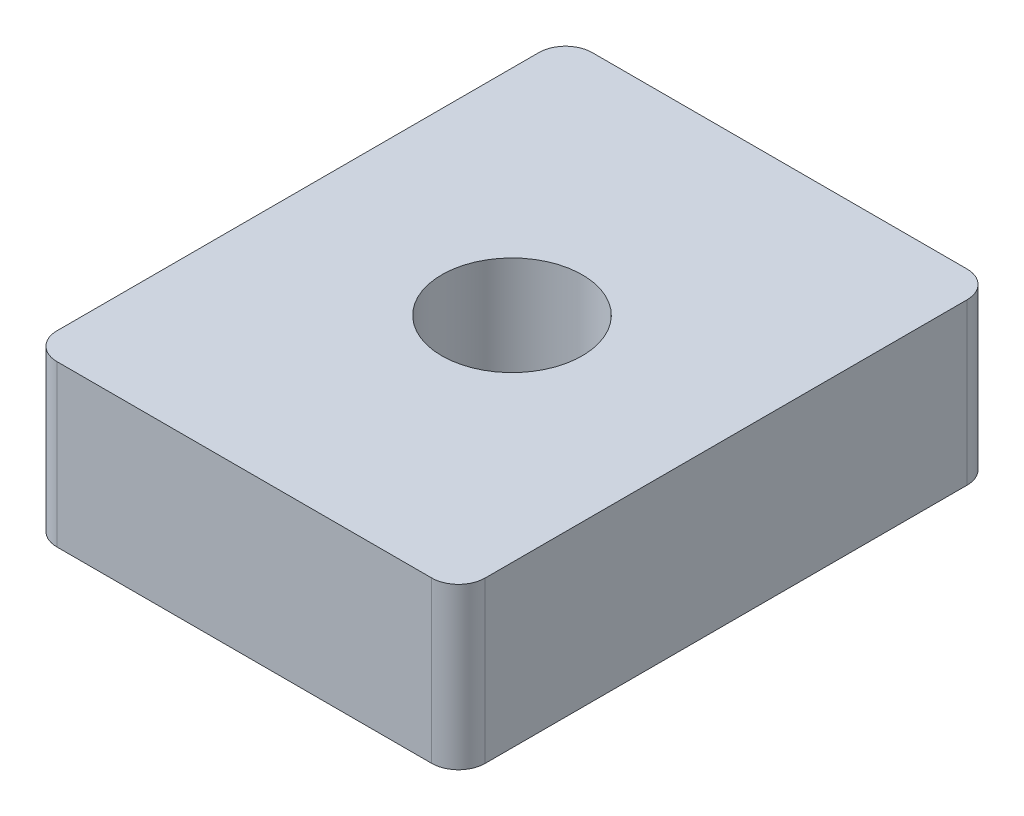
SolidWorks part; units mm, degrees
ref_plane "Front Plane" through (0, 0, 0) normal (0, 0, 1) x (1, 0, 0)
ref_plane "Top Plane" through (0, 0, 0) normal (0, 1, 0) x (1, 0, 0)
ref_plane "Right Plane" through (0, 0, 0) normal (1, 0, 0) x (0, 0, -1)
sketch "Sketch1" plane through (0, 0, 0) normal (0, 1, 0) x (1, 0, 0)
  line L1 (-7, 10) -> (7, 10)
  line L2 (-8, 9) -> (-8, -9)
  line L3 (-7, -10) -> (7, -10)
  line L4 (8, 9) -> (8, -9)
  line L5 (0, -10) -> (0, 10) construction
  line L6 (-8, 0) -> (8, 0) construction
  circle A0 centre (0, 0) radius 2.625
  arc A1 (7, 10) -> (8, 9) centre (7, 9) cw
  arc A2 (8, -9) -> (7, -10) centre (7, -9) cw
  arc A3 (-8, -9) -> (-7, -10) centre (-7, -9) ccw
  arc A4 (-7, 10) -> (-8, 9) centre (-7, 9) ccw
  point P0 (0, 0)
  dimension "D3" = 5.25
  dimension "D4" = 1
  dimension "D1" = 16
  dimension "D2" = 20
extrude "Boss-Extrude1" add sketch "Sketch1" along normal blind 6
